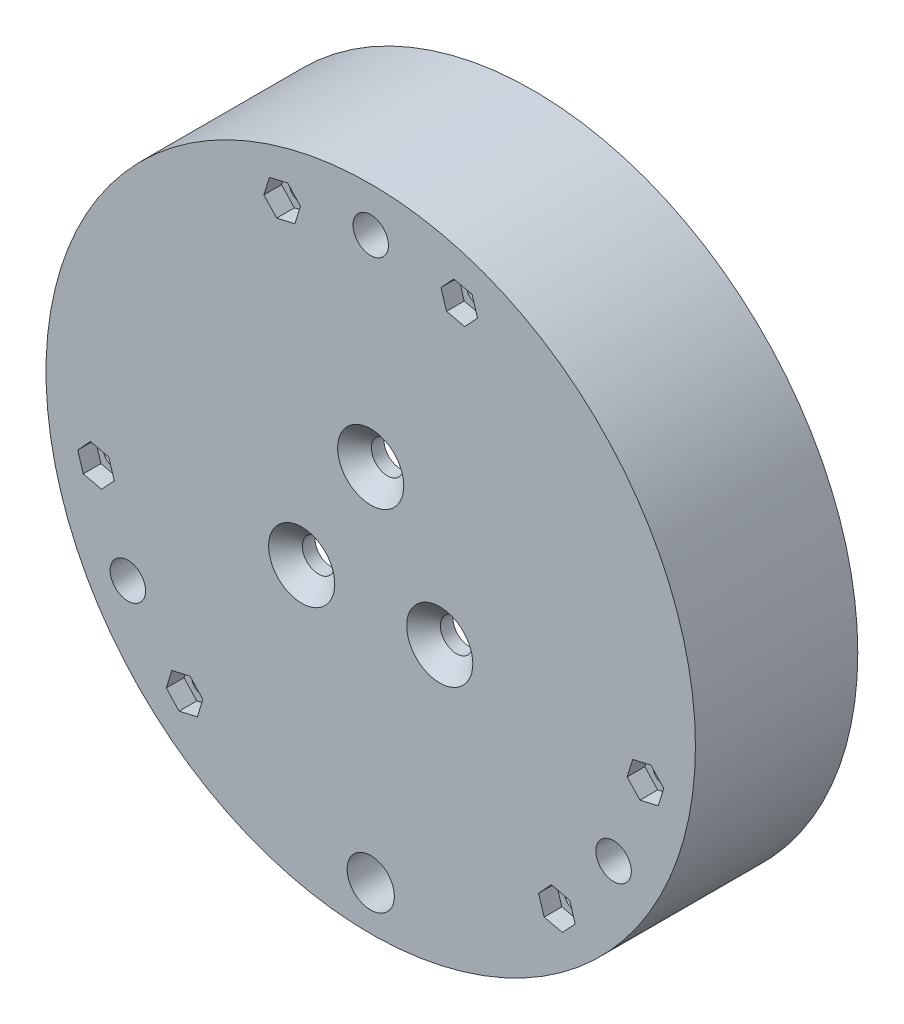
SolidWorks part; units mm, degrees
ref_plane "Alzado" through (0, 0, 0) normal (0, 0, 1) x (1, 0, 0)
ref_plane "Planta" through (0, 0, 0) normal (0, 1, 0) x (1, 0, 0)
ref_plane "Vista lateral" through (0, 0, 0) normal (1, 0, 0) x (0, 0, -1)
sketch "Croquis1" plane through (0, 0, 0) normal (0, 0, 1) x (1, 0, 0)
  circle A0 centre (0, 0) radius 55
  circle A1 centre (0, 0) radius 52.5
  dimension "D1" = 110
  dimension "D2" = 105
extrude "Saliente-Extruir1" add sketch "Croquis1" along normal blind 22.5
sketch "Croquis2" plane through (0, 0, 22.5) normal (0, 0, 1) x (1, 0, 0)
  circle A0 centre (0, 0) radius 55
  dimension "D1" = 110
extrude "Saliente-Extruir2" add sketch "Croquis2" along normal blind 5
sketch "Croquis3" plane through (0, 0, 27.5) normal (0, 0, 1) x (1, 0, 0)
  circle A0 centre (0, 0) radius 13.5
  point P3 (0, 13.5)
  point P4 (11.6913, -6.75)
  point P7 (-11.6913, -6.75)
  point P8 (0, 0)
  dimension "D1" = 27
  dimension "D2" = 3
sketch "Croquis10" plane through (0, 0, 22.5) normal (0, 0, -1) x (-1, 0, 0)
  line L0 (0, 45) -> (0, 51) construction
  line L1 (-3.5, 45) -> (-3.5, 51)
  line L2 (3.5, 45) -> (3.5, 51)
  line L3 (38.9711, -22.5) -> (44.1673, -25.5) construction
  line L4 (40.7211, -19.4689) -> (45.9173, -22.4689)
  line L5 (37.2211, -25.5311) -> (42.4173, -28.5311)
  line L6 (-38.9711, -22.5) -> (-44.1673, -25.5) construction
  line L7 (-37.2211, -25.5311) -> (-42.4173, -28.5311)
  line L8 (-40.7211, -19.4689) -> (-45.9173, -22.4689)
  line L10 (0, -50.0307) -> (0, -38.3709) construction
  line L11 (-4.5, -50.0307) -> (-4.5, -38.3709)
  line L12 (4.5, -50.0307) -> (4.5, -38.3709)
  arc A1 (-3.5, 45) -> (3.5, 45) centre (0, 45) ccw
  arc A2 (-4.5, -50.0307) -> (4.5, -50.0307) centre (0, -50.0307) ccw
  arc A3 (3.5, 51) -> (-3.5, 51) centre (0, 51) ccw
  arc A4 (40.7211, -19.4689) -> (37.2211, -25.5311) centre (38.9711, -22.5) ccw
  arc A5 (42.4173, -28.5311) -> (45.9173, -22.4689) centre (44.1673, -25.5) ccw
  arc A6 (-37.2211, -25.5311) -> (-40.7211, -19.4689) centre (-38.9711, -22.5) ccw
  arc A7 (-45.9173, -22.4689) -> (-42.4173, -28.5311) centre (-44.1673, -25.5) ccw
  arc A8 (4.5, -38.3709) -> (-4.5, -38.3709) centre (0, -38.3709) ccw
  point P6 (0, 48)
  point P15 (0, -44.2008)
  point P17 (41.5692, -24)
  point P24 (-41.5692, -24)
  point P29 (0, 0)
  circle M7 centre (0, 0) radius 52.5
  dimension "D1" = 3.5
  dimension "D4" = 4.5
  dimension "D2" = 6
  dimension "D3" = 3
hole_wizard "Refrentado para tornillo tapón con cabeza plana de clavija de M51" positions "Croquis7" profile "Croquis6" countersink size "M5" standard "Ansi Metric" end condition through all
sketch "Croquis7" plane through (0, 0, 27.5) normal (0, 0, 1) x (1, 0, 0)
  point P0 (0, 13.5)
  point P3 (-11.6913, -6.75)
  point P6 (11.6913, -6.75)
sketch "Croquis6" plane through (0, 13.5, 27.5) normal (1, 0, 0) x (0, -1, 0)
  line L0 (0, 0) -> (0, 27.5)
  line L1 (0, 27.5) -> (2.75, 27.5)
  line L2 (2.75, 27.5) -> (2.75, 2.85)
  line L3 (2.75, 2.85) -> (5.6, 0)
  line L5 (5.6, 0) -> (0, 0)
  line L6 (-2.75, 2.85) -> (-5.6, 0) construction
  line L11 (0, -6.35) -> (0, 107.95) construction
  dimension "Diámetro de taladro hasta el siguiente" = 5.5
  dimension "Profundidad de taladro hasta el siguiente" = 27.5
  dimension "Diámetro de avellanado cercano" = 11.2
  dimension "Ángulo de avellanado cercano" = 90
extrude "Saliente-Extruir8" add sketch "Croquis10" along normal blind 10 contours L12 A8 L11 A2 M7 | L5 A5 L4 A4 | L7 A7 L8 A6 | L1 A3 L2 A1
sketch "Croquis12" plane through (0, 0, 27.5) normal (0, 0, 1) x (1, 0, 0)
  line L0 (0, 47.5) -> (0, 52.082) construction
  line L1 (-11.8522, 45.4873) -> (-13.788, 48.0044)
  line L2 (-13.788, 48.0044) -> (-16.9358, 47.5865)
  line L3 (-16.9358, 47.5865) -> (-18.1478, 44.6515)
  line L4 (-18.1478, 44.6515) -> (-16.212, 42.1344)
  line L5 (-16.212, 42.1344) -> (-13.0642, 42.5522)
  line L6 (-13.0642, 42.5522) -> (-11.8522, 45.4873)
  line L7 (18.1478, 44.6515) -> (16.212, 42.1344)
  line L8 (16.9358, 47.5865) -> (18.1478, 44.6515)
  line L9 (13.788, 48.0044) -> (16.9358, 47.5865)
  line L10 (11.8522, 45.4873) -> (13.788, 48.0044)
  line L11 (13.0642, 42.5522) -> (11.8522, 45.4873)
  line L12 (16.212, 42.1344) -> (13.0642, 42.5522)
  circle A0 centre (0, 0) radius 47.5
  circle A1 centre (0, 47.5) radius 3
  circle A2 centre (41.1362, -23.75) radius 3
  circle A3 centre (-41.1362, -23.75) radius 3
  circle A4 centre (0, -47.5) radius 4
  circle A5 centre (-15, 45.0694) radius 2.75 construction
  circle A6 centre (15, 45.0694) radius 2.75 construction
  point P12 (0, 0)
  dimension "D1" = 95
  dimension "D2" = 6
  dimension "D4" = 8
  dimension "D5" = 5.5
  dimension "D6" = 15
  dimension "D3" = 3
extrude "Cortar-Extruir4" cut sketch "Croquis12" against normal blind 10 contours A3 | A2 | A1 | A4
sketch "Croquis15" plane through (0, 0, 27.5) normal (0, 0, 1) x (1, 0, 0)
  line L0 (0, 47.5) -> (0, 53.6415) construction
  line L1 (-11.905, 45.7795) -> (-14.0675, 48.1048)
  line L2 (-14.0675, 48.1048) -> (-17.1625, 47.3947)
  line L3 (-17.1625, 47.3947) -> (-18.095, 44.3593)
  line L4 (-18.095, 44.3593) -> (-15.9325, 42.034)
  line L5 (-15.9325, 42.034) -> (-12.8375, 42.7441)
  line L6 (-12.8375, 42.7441) -> (-11.905, 45.7795)
  line L7 (18.095, 44.3593) -> (15.9325, 42.034)
  line L8 (12.8375, 42.7441) -> (11.905, 45.7795)
  line L9 (15.9325, 42.034) -> (12.8375, 42.7441)
  line L10 (17.1625, 47.3947) -> (18.095, 44.3593)
  line L11 (14.0675, 48.1048) -> (17.1625, 47.3947)
  line L12 (11.905, 45.7795) -> (14.0675, 48.1048)
  line L13 (44.3688, -7.219) -> (43.4362, -10.2544)
  line L14 (43.4362, -10.2544) -> (45.5987, -12.5797)
  line L15 (45.5987, -12.5797) -> (48.6937, -11.8696)
  line L16 (48.6937, -11.8696) -> (49.6262, -8.8342)
  line L17 (49.6262, -8.8342) -> (47.4638, -6.5089)
  line L18 (47.4638, -6.5089) -> (44.3688, -7.219)
  line L19 (34.6262, -36.2352) -> (32.4638, -38.5605)
  line L20 (33.6937, -33.1998) -> (34.6262, -36.2352)
  line L21 (30.5987, -32.4897) -> (33.6937, -33.1998)
  line L22 (28.4362, -34.815) -> (30.5987, -32.4897)
  line L23 (29.3688, -37.8504) -> (28.4362, -34.815)
  line L24 (32.4638, -38.5605) -> (29.3688, -37.8504)
  line L25 (-28.4362, -34.815) -> (-30.5987, -32.4897)
  line L26 (-30.5987, -32.4897) -> (-33.6937, -33.1998)
  line L27 (-33.6937, -33.1998) -> (-34.6262, -36.2352)
  line L28 (-34.6262, -36.2352) -> (-32.4638, -38.5605)
  line L29 (-32.4638, -38.5605) -> (-29.3688, -37.8504)
  line L30 (-29.3688, -37.8504) -> (-28.4362, -34.815)
  line L31 (-48.6937, -11.8696) -> (-49.6262, -8.8342)
  line L32 (-45.5987, -12.5797) -> (-48.6937, -11.8696)
  line L33 (-43.4362, -10.2544) -> (-45.5987, -12.5797)
  line L34 (-44.3688, -7.219) -> (-43.4362, -10.2544)
  line L35 (-47.4638, -6.5089) -> (-44.3688, -7.219)
  line L36 (-49.6262, -8.8342) -> (-47.4638, -6.5089)
  circle A0 centre (0, 0) radius 47.5
  circle A1 centre (-15, 45.0694) radius 2.75 construction
  circle A2 centre (0, 47.5) radius 3
  circle A3 centre (15, 45.0694) radius 2.75 construction
  point P50 (0, 0)
  dimension "D1" = 5.5
  dimension "D2" = 6
  dimension "D3" = 15
  dimension "D4" = 3
extrude "Cortar-Extruir6" cut sketch "Croquis15" against normal blind 3 contours L32 L31 L36 L35 L34 L33 | L29 L30 L25 L26 L27 L28 | L19 L24 L23 L22 L21 L20 | L16 L17 L18 L13 L14 L15 | L3 L4 L5 L6 L1 L2 | L11 L10 L7 L9 L8 L12
sketch "Croquis16" plane through (0, 0, 27.5) normal (0, 0, 1) x (1, 0, 0)
  line L0 (0, 44.5) -> (0, 53.0661) construction
  circle A0 centre (-15.0036, 45.0889) radius 1.75
  circle A1 centre (0, 47.5) radius 3 construction
  circle A2 centre (15.0036, 45.0889) radius 1.75
  circle A3 centre (46.5499, -9.551) radius 1.75
  circle A4 centre (31.5464, -35.5379) radius 1.75
  circle A5 centre (-31.5464, -35.5379) radius 1.75
  circle A6 centre (-46.5499, -9.551) radius 1.75
  point P21 (0, 0)
  dimension "D1" = 3.5
  dimension "D2" = 3
extrude "Cortar-Extruir7" cut sketch "Croquis16" against normal blind 5
